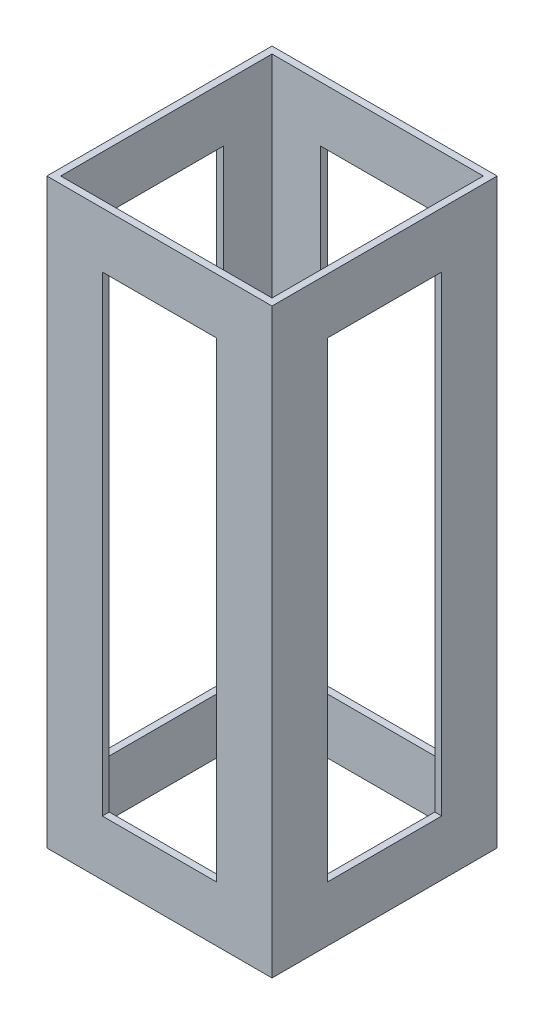
SolidWorks part; units mm, degrees
material "6061-T6 (SS)"
ref_plane "Front Plane" through (0, 0, 0) normal (0, 0, 1) x (1, 0, 0)
ref_plane "Top Plane" through (0, 0, 0) normal (0, 1, 0) x (1, 0, 0)
ref_plane "Right Plane" through (0, 0, 0) normal (1, 0, 0) x (0, 0, -1)
sketch "Sketch1" plane through (0, 0, 0) normal (0, 1, 0) x (1, 0, 0)
  line L0 (-48.4188, 48.4187) -> (48.4187, 48.4187)
  line L1 (-51.5938, -51.5938) -> (51.5937, -51.5938)
  line L2 (-51.5938, -51.5938) -> (-51.5938, 51.5937)
  line L3 (-51.5938, 51.5937) -> (51.5937, 51.5937)
  line L4 (51.5937, -51.5938) -> (51.5937, 51.5937)
  line L5 (-51.5938, -51.5938) -> (51.5937, 51.5937) construction
  line L6 (-51.5938, 51.5937) -> (51.5937, -51.5938) construction
  line L7 (48.4187, -48.4188) -> (48.4187, 48.4187)
  line L8 (-48.4188, -48.4188) -> (48.4187, -48.4188)
  line L9 (-48.4188, -48.4188) -> (-48.4188, 48.4187)
  point P0 (0, 0)
  dimension "D1" = 103.1875
  dimension "D2" = 3.175
extrude "Boss-Extrude1" add sketch "Sketch1" along normal blind 266.7
sketch "Sketch2" plane through (0, 0, 0) normal (0, 0, 1) x (1, 0, 0)
  line L0 (26.1937, 241.3) -> (-26.1938, 241.3)
  line L1 (-26.1938, 241.3) -> (-26.1938, 25.4)
  line L2 (-26.1938, 25.4) -> (26.1937, 25.4)
  line L3 (26.1937, 25.4) -> (26.1937, 241.3)
  line L4 (-51.5938, 0) -> (51.5937, 0)
  line L5 (51.5937, 0) -> (51.5937, 266.7)
  line L6 (51.5937, 266.7) -> (-51.5938, 266.7)
  line L7 (-51.5938, 266.7) -> (-51.5938, 0)
  line L8 (-51.5938, 0) -> (51.5937, 0) construction
  line L9 (51.5937, 0) -> (51.5937, 266.7) construction
  line L10 (51.5937, 266.7) -> (-51.5938, 266.7) construction
  line L11 (-51.5938, 266.7) -> (-51.5938, 0) construction
  dimension "D1" = 0
  dimension "D2" = 25.4
extrude "Cut-Extrude2" cut sketch "Sketch2" against normal through all both and the other way through all
sketch "Sketch3" plane through (0, 0, 0) normal (1, 0, 0) x (0, 0, -1)
  line L4 (-51.5938, 0) -> (51.5937, 0)
  line L5 (51.5937, 0) -> (51.5937, 266.7)
  line L6 (51.5937, 266.7) -> (-51.5938, 266.7)
  line L7 (-51.5938, 266.7) -> (-51.5938, 0)
  line L8 (-51.5938, 0) -> (51.5937, 0) construction
  line L9 (51.5937, 0) -> (51.5937, 266.7) construction
  line L10 (51.5937, 266.7) -> (-51.5938, 266.7) construction
  line L11 (-51.5938, 266.7) -> (-51.5938, 0) construction
  line L16 (-26.1938, 25.4) -> (26.1937, 25.4)
  line L17 (26.1937, 25.4) -> (26.1937, 241.3)
  line L18 (26.1937, 241.3) -> (-26.1938, 241.3)
  line L19 (-26.1938, 241.3) -> (-26.1938, 25.4)
  line L20 (-26.1938, 25.4) -> (26.1937, 25.4)
  line L21 (26.1937, 25.4) -> (26.1937, 241.3)
  line L22 (26.1937, 241.3) -> (-26.1938, 241.3)
  line L23 (-26.1938, 241.3) -> (-26.1938, 25.4)
  dimension "D1" = 0
  dimension "D2" = 25.4
extrude "Cut-Extrude3" cut sketch "Sketch3" against normal through all both and the other way through all
